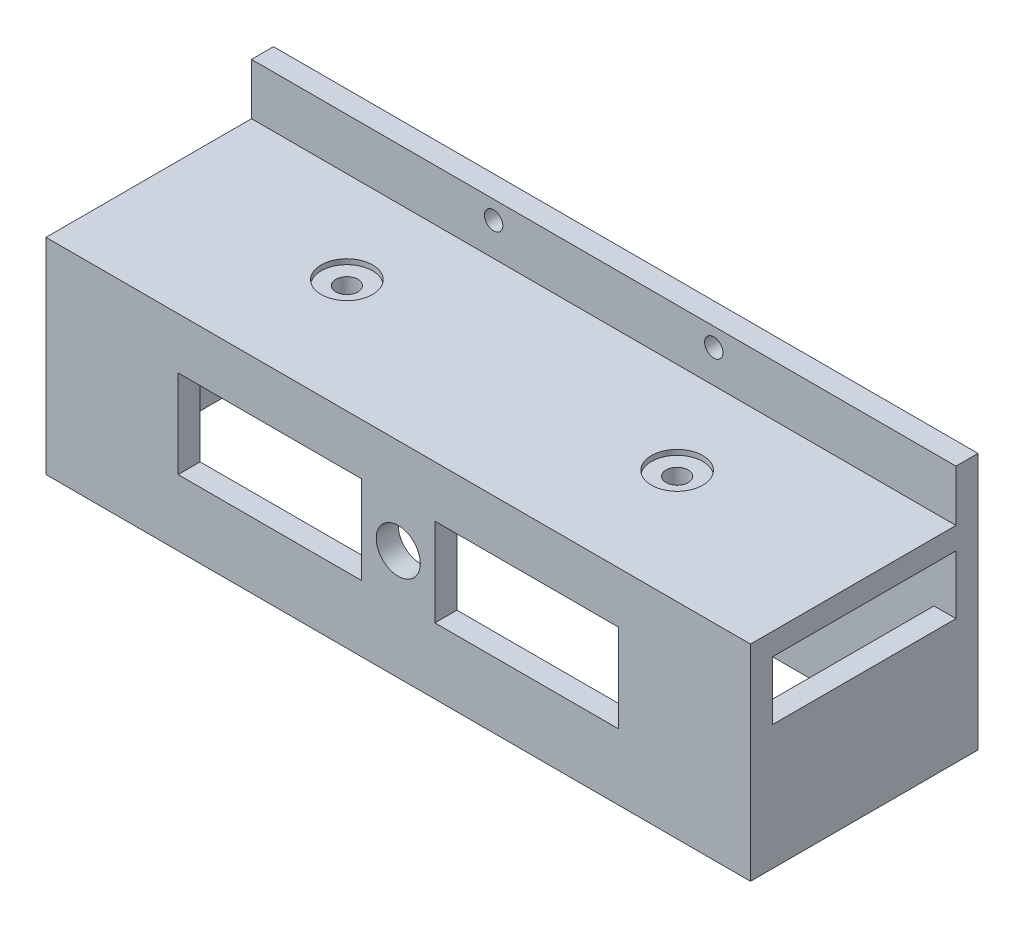
SolidWorks part; units mm, degrees
ref_plane "Front Plane" through (0, 0, 0) normal (0, 0, 1) x (1, 0, 0)
ref_plane "Top Plane" through (0, 0, 0) normal (0, 1, 0) x (1, 0, 0)
ref_plane "Right Plane" through (0, 0, 0) normal (1, 0, 0) x (0, 0, -1)
sketch "Sketch1" plane through (0, 0, 0) normal (0, 1, 0) x (1, 0, 0)
  line L1 (-45.3289, -147.8611) -> (50.6711, -147.8611)
  line L2 (-45.3289, -147.8611) -> (-45.3289, -175.8611)
  line L3 (-45.3289, -175.8611) -> (50.6711, -175.8611)
  line L4 (50.6711, -147.8611) -> (50.6711, -175.8611)
  dimension "D1" = 96
  dimension "D2" = 28
extrude "Boss-Extrude1" add sketch "Sketch1" along normal blind 3
sketch "Sketch2" plane through (0, 0, 0) normal (0, -1, 0) x (-1, 0, 0)
  line L0 (45.3289, -175.8611) -> (-50.6711, -175.8611) construction
  line L1 (45.3289, -175.8611) -> (-50.6711, -175.8611)
  line L2 (45.3289, -175.8611) -> (45.3289, -172.8611)
  line L3 (45.3289, -172.8611) -> (-50.6711, -172.8611)
  line L4 (-50.6711, -175.8611) -> (-50.6711, -172.8611)
  line L5 (-50.6711, -175.8611) -> (-50.6711, -147.8611) construction
  line L6 (-50.6711, -147.8611) -> (45.3289, -147.8611) construction
  line L7 (45.3289, -172.8611) -> (42.3289, -172.8611)
  line L8 (45.3289, -172.8611) -> (45.3289, -147.8611)
  line L9 (45.3289, -147.8611) -> (42.3289, -147.8611)
  line L10 (42.3289, -172.8611) -> (42.3289, -147.8611)
  line L12 (-50.6711, -172.8611) -> (-47.6711, -172.8611)
  line L13 (-50.6711, -172.8611) -> (-50.6711, -147.8611)
  line L14 (-50.6711, -147.8611) -> (-47.6711, -147.8611)
  line L15 (-47.6711, -172.8611) -> (-47.6711, -147.8611)
  line M5 (45.3289, -175.8611) -> (45.3289, -147.8611)
  line M6 (45.3289, -147.8611) -> (-50.6711, -147.8611)
  line M7 (-50.6711, -147.8611) -> (-50.6711, -175.8611)
  line M8 (-50.6711, -175.8611) -> (45.3289, -175.8611)
  dimension "D1" = 96
  dimension "D2" = 0
  dimension "D3" = 0
  dimension "D4" = 3
  dimension "D5" = 0
  dimension "D6" = 3
  dimension "D7" = 0
  dimension "D8" = 3
extrude "Boss-Extrude2" add sketch "Sketch2" along normal blind 25 contours L3 M5 M7 M8 | L10 L3 M5 M6 | L3 L15 M6 M7
sketch "Sketch3" plane through (0, 0, 147.8611) normal (0, 0, -1) x (-1, 0, 0)
  line L1 (-50.6711, 10) -> (45.3289, 10)
  line L2 (-50.6711, 10) -> (-50.6711, -25)
  line L3 (-50.6711, -25) -> (45.3289, -25)
  line L4 (45.3289, 10) -> (45.3289, -25)
  line L5 (-50.6711, 3) -> (-50.6711, -25) construction
  line L6 (-47.6711, -25) -> (-50.6711, -25) construction
  line L7 (-50.6711, 3) -> (45.3289, 3) construction
  dimension "D1" = 96
  dimension "D2" = 7
  dimension "D3" = 0
  dimension "D4" = 0
extrude "Boss-Extrude3" add sketch "Sketch3" along normal blind 3
sketch "Sketch4" plane through (0, 3, 0) normal (0, 1, 0) x (1, 0, 0)
  line L0 (-45.3289, -147.8611) -> (-45.3289, -175.8611) construction
  line L3 (-45.3289, -175.8611) -> (50.6711, -175.8611) construction
  circle A0 centre (-19.8289, -160.3611) radius 1.5
  circle A1 centre (25.1711, -160.3611) radius 1.5
  dimension "D4" = 3
  dimension "D5" = 3
  dimension "D1" = 25.5
  dimension "D2" = 45
  dimension "D3" = 15.5
  dimension "D6" = 15.5
extrude "Cut-Extrude2" cut sketch "Sketch4" against normal up to next contours A0 | A1
sketch "Sketch5" plane through (0, 3, 0) normal (0, 1, 0) x (1, 0, 0)
  circle A0 centre (-19.8289, -160.3611) radius 3.5
  circle A1 centre (25.1711, -160.3611) radius 3.5
  circle A2 centre (25.1711, -160.3611) radius 1.5 construction
  circle A3 centre (-19.8289, -160.3611) radius 1.5 construction
  dimension "D1" = 7
  dimension "D2" = 7
  dimension "D3" = 0
extrude "Cut-Extrude3" cut sketch "Sketch5" against normal blind 0.7
sketch "Sketch6" plane through (0, 0, 144.8611) normal (0, 0, -1) x (-1, 0, 0)
  line L0 (-50.6711, 10) -> (-50.6711, -25) construction
  line L2 (-50.6711, -25) -> (45.3289, -25) construction
  circle A0 centre (-18.9211, -2) radius 1.5
  circle A1 centre (13.5789, -2) radius 1.5
  circle A2 centre (12.3289, 7.5) radius 1.25
  circle A3 centre (-17.6711, 7.5) radius 1.25
  dimension "D1" = 3
  dimension "D2" = 3
  dimension "D7" = 2.5
  dimension "D8" = 2.5
  dimension "D3" = 32.5
  dimension "D4" = 31.75
  dimension "D5" = 23
  dimension "D6" = 23
  dimension "D9" = 30
  dimension "D10" = 33
  dimension "D11" = 9.5
  dimension "D12" = 9.5
extrude "Cut-Extrude4" cut sketch "Sketch6" against normal up to next
sketch "Sketch7" plane through (0, 0, 147.8611) normal (0, 0, 1) x (1, 0, 0)
  circle A0 centre (18.9211, -2) radius 4
  circle A1 centre (-13.5789, -2) radius 4
  circle A3 centre (18.9211, -2) radius 1.5 construction
  circle A4 centre (-13.5789, -2) radius 1.5 construction
  dimension "D1" = 8
  dimension "D2" = 8
extrude "Cut-Extrude5" cut sketch "Sketch7" against normal blind 2
sketch "Sketch8" plane through (0, 0, 175.8611) normal (0, 0, 1) x (1, 0, 0)
  line L0 (-45.3289, 3) -> (-45.3289, -25) construction
  line L1 (50.6711, -25) -> (-45.3289, -25) construction
  line L3 (-27.3289, -16) -> (-2.3289, -16)
  line L4 (-27.3289, -16) -> (-27.3289, -4)
  line L5 (-27.3289, -4) -> (-2.3289, -4)
  line L6 (-2.3289, -16) -> (-2.3289, -4)
  line L7 (7.6711, -16) -> (32.6711, -16)
  line L8 (7.6711, -16) -> (7.6711, -4)
  line L9 (7.6711, -4) -> (32.6711, -4)
  line L10 (32.6711, -16) -> (32.6711, -4)
  circle A0 centre (2.6711, -10) radius 3
  dimension "D1" = 6
  dimension "D2" = 48
  dimension "D3" = 15
  dimension "D4" = 12
  dimension "D5" = 25
  dimension "D6" = 25
  dimension "D7" = 12
  dimension "D8" = 10
  dimension "D9" = 18
  dimension "D10" = 9
  dimension "D11" = 9
extrude "Cut-Extrude7" cut sketch "Sketch8" against normal up to next contours A0 | L3 L6 L5 L4 | L8 L7 L10 L9
sketch "Sketch9" plane through (0, 0, 147.8611) normal (0, 0, 1) x (1, 0, 0)
  line L0 (47.6711, 0) -> (22.3852, 0) construction
  line L1 (33.6711, -17) -> (24.6711, -17)
  line L2 (33.6711, -17) -> (33.6711, -7)
  line L3 (33.6711, -7) -> (24.6711, -7)
  line L4 (24.6711, -17) -> (24.6711, -7)
  line L5 (12.6711, -17) -> (-7.3289, -17)
  line L6 (12.6711, -17) -> (12.6711, -7)
  line L7 (12.6711, -7) -> (-7.3289, -7)
  line L8 (-7.3289, -17) -> (-7.3289, -7)
  line L9 (-19.3289, -17) -> (-28.3289, -17)
  line L10 (-19.3289, -17) -> (-19.3289, -7)
  line L11 (-19.3289, -7) -> (-28.3289, -7)
  line L12 (-28.3289, -17) -> (-28.3289, -7)
  line L13 (47.6711, -25) -> (47.6711, 0) construction
  line L14 (-42.3289, -25) -> (-42.3289, 0) construction
  dimension "D1" = 10
  dimension "D2" = 10
  dimension "D3" = 10
  dimension "D4" = 7
  dimension "D5" = 7
  dimension "D6" = 7
  dimension "D7" = 14
  dimension "D8" = 14
  dimension "D9" = 9
  dimension "D10" = 9
  dimension "D11" = 20
  dimension "D12" = 12
extrude "Cut-Extrude8" cut sketch "Sketch9" against normal up to next contours L8 L5 L6 L7 | L12 L9 L10 L11 | L2 L1 L4 L3
sketch "Sketch10" plane through (47.6711, 0, 0) normal (-1, 0, 0) x (0, 0, 1)
  line L0 (172.8611, 0) -> (147.8611, 0) construction
  line L1 (147.8611, -8) -> (172.8611, -8)
  line L2 (147.8611, -8) -> (147.8611, 0)
  line L3 (147.8611, 0) -> (172.8611, 0)
  line L4 (172.8611, -8) -> (172.8611, 0)
  line L5 (147.8611, -25) -> (147.8611, 0) construction
  line L6 (172.8611, -25) -> (172.8611, 0) construction
  dimension "D1" = 8
  dimension "D2" = 0
  dimension "D3" = 0
  dimension "D4" = 0
extrude "Cut-Extrude9" cut sketch "Sketch10" against normal up to next contours L2 L1 L4 L3
